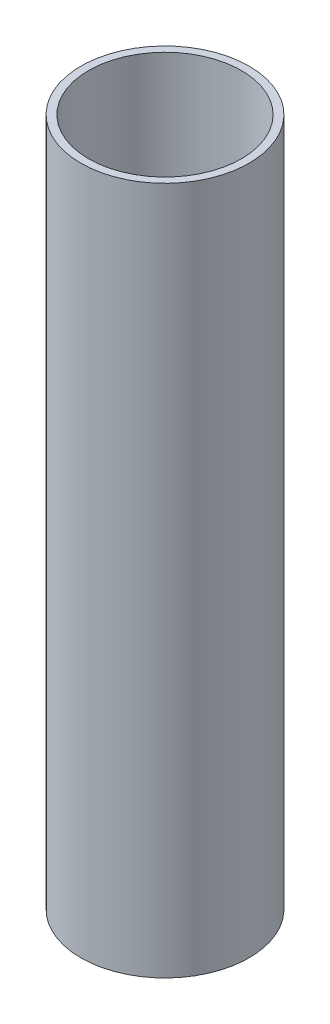
SolidWorks part; units mm, degrees
ref_plane "前视基准面" through (0, 0, 0) normal (0, 0, 1) x (1, 0, 0)
ref_plane "上视基准面" through (0, 0, 0) normal (0, 1, 0) x (1, 0, 0)
ref_plane "右视基准面" through (0, 0, 0) normal (1, 0, 0) x (0, 0, -1)
sketch "草图1" plane through (0, 0, 0) normal (0, 1, 0) x (1, 0, 0)
  circle A0 centre (0, 0) radius 11
  circle A1 centre (0, 0) radius 10
  dimension "D1" = 20
  dimension "D2" = 22
extrude "凸台-拉伸1" add sketch "草图1" along normal blind 90
